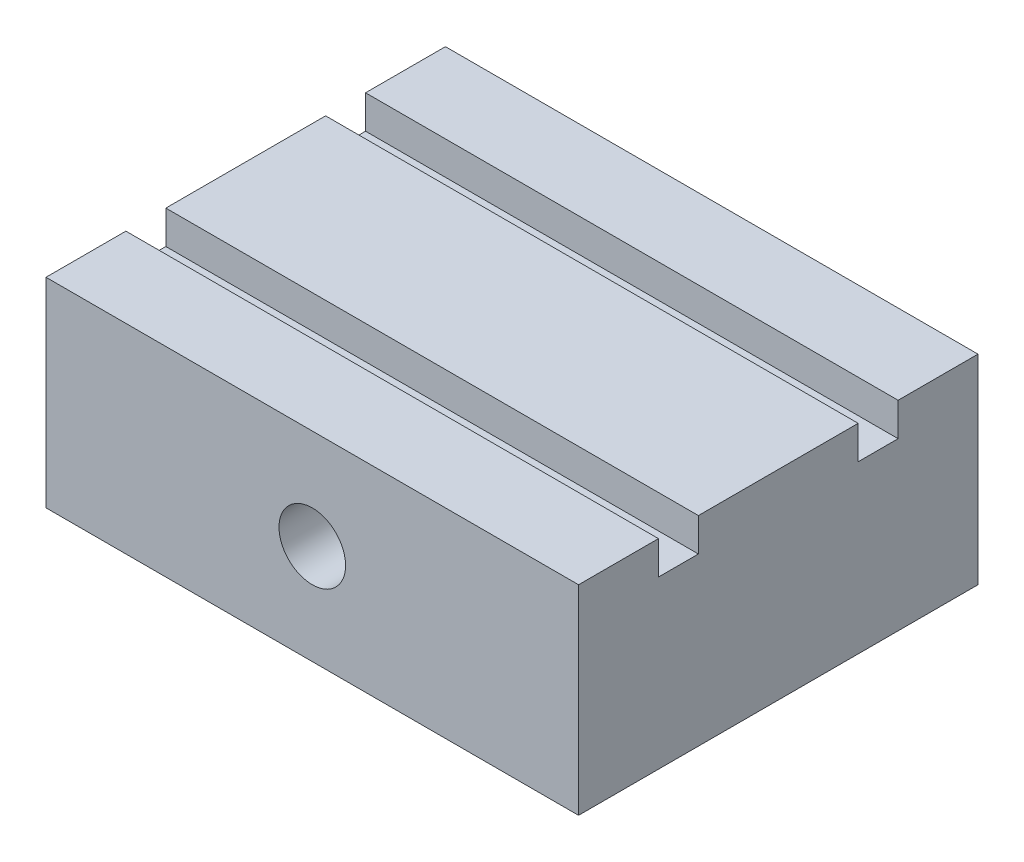
SolidWorks part; units mm, degrees
ref_plane "前视基准面" through (0, 0, 0) normal (0, 0, 1) x (1, 0, 0)
ref_plane "上视基准面" through (0, 0, 0) normal (0, 1, 0) x (1, 0, 0)
ref_plane "右视基准面" through (0, 0, 0) normal (1, 0, 0) x (0, 0, -1)
sketch "草图1" plane through (0, 0, 0) normal (0, 1, 0) x (1, 0, 0)
  line L1 (-40, 30) -> (40, 30)
  line L2 (-40, 30) -> (-40, -30)
  line L3 (-40, -30) -> (40, -30)
  line L4 (40, 30) -> (40, -30)
  line L5 (-40, 30) -> (40, -30) construction
  line L6 (-40, -30) -> (40, 30) construction
  point P0 (0, 0)
  dimension "D1" = 80
  dimension "D2" = 60
extrude "凸台-拉伸1" add sketch "草图1" along normal blind 30
sketch "草图2" plane through (0, 0, 30) normal (0, 0, 1) x (1, 0, 0)
  line L0 (-40, 30) -> (40, 0) construction
  line L1 (40, 30) -> (-40, 0) construction
  circle A0 centre (0, 15) radius 5
  dimension "D1" = 10
extrude "切除-拉伸1" cut sketch "草图2" against normal through all
sketch "草图3" plane through (0, 30, 0) normal (0, 1, 0) x (1, 0, 0)
  line L0 (-40, 30) -> (-40, -30) construction
  line L1 (-40, 18) -> (40, 18)
  line L2 (-40, 18) -> (-40, 12)
  line L3 (-40, 12) -> (40, 12)
  line L4 (40, 18) -> (40, 12)
  line L5 (40, -30) -> (40, 30) construction
  line L6 (0, 0) -> (50.3711, 0) construction
  line L7 (-40, -12) -> (40, -12)
  line L8 (40, -18) -> (40, -12)
  line L9 (-40, -18) -> (40, -18)
  line L10 (-40, -18) -> (-40, -12)
  dimension "D1" = 24
  dimension "D2" = 36
extrude "切除-拉伸2" cut sketch "草图3" against normal blind 5
